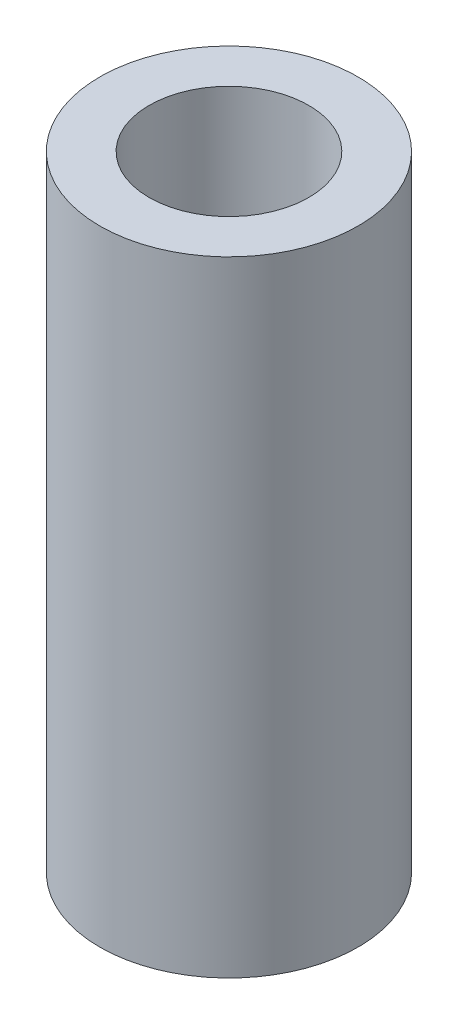
SolidWorks part; units mm, degrees
material "Markforged"
ref_plane "Front Plane" through (0, 0, 0) normal (0, 0, 1) x (1, 0, 0)
ref_plane "Top Plane" through (0, 0, 0) normal (0, 1, 0) x (1, 0, 0)
ref_plane "Right Plane" through (0, 0, 0) normal (1, 0, 0) x (0, 0, -1)
sketch "Sketch1" plane through (0, 0, 0) normal (0, 1, 0) x (1, 0, 0)
  circle A0 centre (0, 0) radius 2.159
  circle A1 centre (0, 0) radius 3.4925
  dimension "D1" = 4.318
  dimension "D2" = 6.985
extrude "Boss-Extrude1" add sketch "Sketch1" along normal mid plane 16.891
